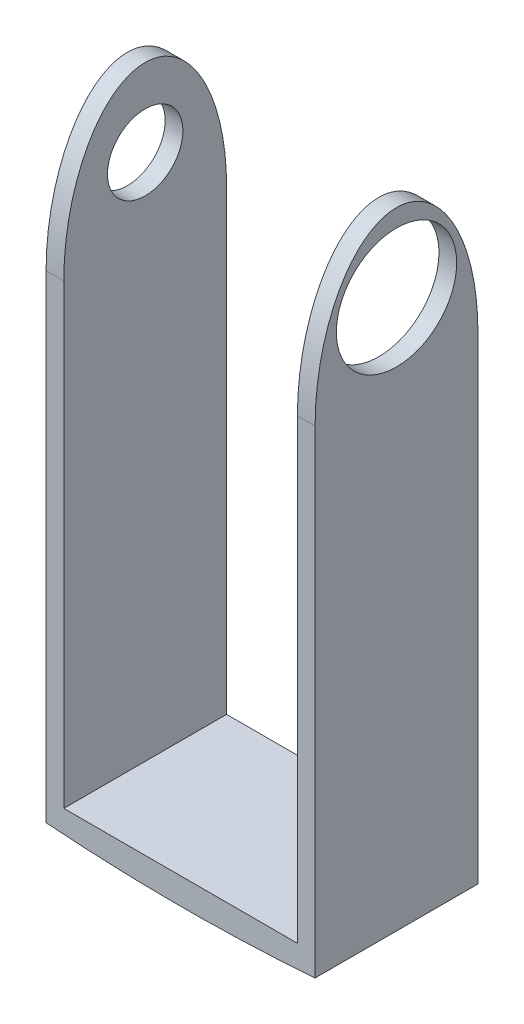
SolidWorks part; units mm, degrees
ref_plane "Front Plane" through (0, 0, 0) normal (0, 0, 1) x (1, 0, 0)
ref_plane "Top Plane" through (0, 0, 0) normal (0, 1, 0) x (1, 0, 0)
ref_plane "Right Plane" through (0, 0, 0) normal (1, 0, 0) x (0, 0, -1)
sketch "Sketch1" plane through (0, 0, 0) normal (0, 0, 1) x (1, 0, 0)
  line L0 (-3.3539, 20.1872) -> (-3.3539, -2.2918)
  line L1 (-3.3539, -2.2918) -> (6.2981, -2.2918)
  line L2 (6.2981, -2.2918) -> (6.2981, 20.1872)
  line L3 (5.6631, 20.1872) -> (5.6631, -1.5298)
  line L4 (5.6631, -1.5298) -> (-2.7189, -1.5298)
  line L5 (-2.7189, -1.5298) -> (-2.7189, 20.1872)
  line L6 (-2.7189, 20.1872) -> (-3.3539, 20.1872)
  line L7 (5.6631, 20.1872) -> (6.2981, 20.1872)
  dimension "D1" = 8.382
  dimension "D2" = 9.652
  dimension "D3" = 0.635
  dimension "D4" = 21.717
  dimension "D5" = 22.479
  dimension "D6" = 21.717
extrude "Boss-Extrude1" add sketch "Sketch1" along normal blind 5.842
sketch "Sketch2" plane through (-3.3539, 0, 0) normal (-1, 0, 0) x (0, 0, 1)
  line L0 (5.842, 20.1872) -> (0, 20.1872) construction
  line L1 (2.921, -2.2918) -> (2.921, 20.1872) construction
  point P0 (2.921, 17.3932)
  dimension "D1" = 2.794
hole_wizard "#6-32 Tapped Hole1" positions "Sketch3" profile "Sketch4" tap size "#6-32" standard "ANSI Inch" end condition up to next
sketch "Sketch3" plane through (-3.3539, 0, 0) normal (-1, 0, 0) x (0, 0, 1)
  point P0 (2.921, 17.3932)
sketch "Sketch4" plane through (-3.3539, 17.3932, 2.921) normal (0, 1, 0) x (0, 0, 1)
  line L0 (0, 0) -> (0, 0.635)
  line L1 (0, 0.635) -> (1.3525, 0.635)
  line L2 (1.3525, 0.635) -> (1.3525, 0)
  line L5 (1.3525, 0) -> (0, 0)
  line L11 (0, -6.35) -> (0, 107.95) construction
  dimension "Thread Major Dia." = 2.7051
  dimension "Thru Tap Drill Depth" = 0.635
sketch "Sketch5" plane through (6.2981, 0, 0) normal (1, 0, 0) x (0, 0, -1)
  point P0 (-2.921, 17.3932)
sketch "Sketch6" plane through (6.2981, 0, 0) normal (1, 0, 0) x (0, 0, -1)
  circle A0 centre (-2.921, 17.3932) radius 2.159
extrude "Cut-Extrude1" cut sketch "Sketch6" against normal up to next
sketch "Sketch12" plane through (-3.3539, 0, 0) normal (-1, 0, 0) x (0, 0, 1)
  line L0 (2.921, -2.2918) -> (2.921, 20.1872) construction
  line L1 (5.842, -2.2918) -> (0, -2.2918) construction
  line L2 (5.842, 20.1872) -> (0, 20.1872) construction
sketch "Sketch13" plane through (0, 0, 0) normal (0, 0, 1) x (1, 0, 0)
  line L0 (6.2981, -2.2918) -> (1.4721, 60.2603) construction
  line L1 (1.4721, 60.2603) -> (-3.3539, -2.2918) construction
  dimension "D1" = 62.738
  dimension "D2" = 62.738
sketch "Sketch15" plane through (0, 0, 0) normal (0, 0, 1) x (1, 0, 0)
  line L0 (-3.3539, -2.2918) -> (6.2981, -2.2918) construction
  line L1 (6.2981, -2.2918) -> (-3.3539, -2.2918)
  arc A0 (-3.3539, -2.2918) -> (6.2981, -2.2918) centre (1.4721, 60.2603) ccw
extrude "Boss-Extrude2" add sketch "Sketch15" along normal through all
sketch "Sketch18" plane through (-3.3539, 0, 0) normal (-1, 0, 0) x (0, 0, 1)
  line L0 (2.921, -2.2918) -> (2.921, 20.1872) construction
  point P0 (2.921, 11.1176)
  point P1 (2.921, 8.9477)
sketch "Sketch25" plane through (-3.3539, 0, 0) normal (-1, 0, 0) x (0, 0, 1)
  line L0 (2.921, -2.2918) -> (2.921, 20.1872) construction
  point P0 (2.921, 13.3767)
sketch "Sketch28" plane through (6.2981, 0, 0) normal (1, 0, 0) x (0, 0, -1)
  line L0 (-2.921, -2.2918) -> (-2.921, 20.1872) construction
  line L1 (0, 60.2603) -> (0, -2.2918) construction
  line L2 (-5.842, -2.2918) -> (-5.842, 20.1872) construction
  line L3 (-5.842, 14.8606) -> (-5.842, 20.1872)
  line L4 (-5.842, 20.1872) -> (0, 20.1872)
  line L5 (0, 20.1872) -> (0, 14.8606)
  ellipse E0 centre (-2.921, 14.8606) end of major axis (-2.921, 20.1872) minor radius 2.921 (0, 14.8606) -> (-5.842, 14.8606) ccw
  line M6 (0, -2.2918) -> (0, 20.1872)
  line M7 (0, 20.1872) -> (-5.842, 20.1872)
  line M8 (-5.842, 20.1872) -> (-5.842, -2.2918)
extrude "Cut-Extrude4" cut sketch "Sketch28" against normal through all contours E0 L4 M8 | E0 M6 M7
